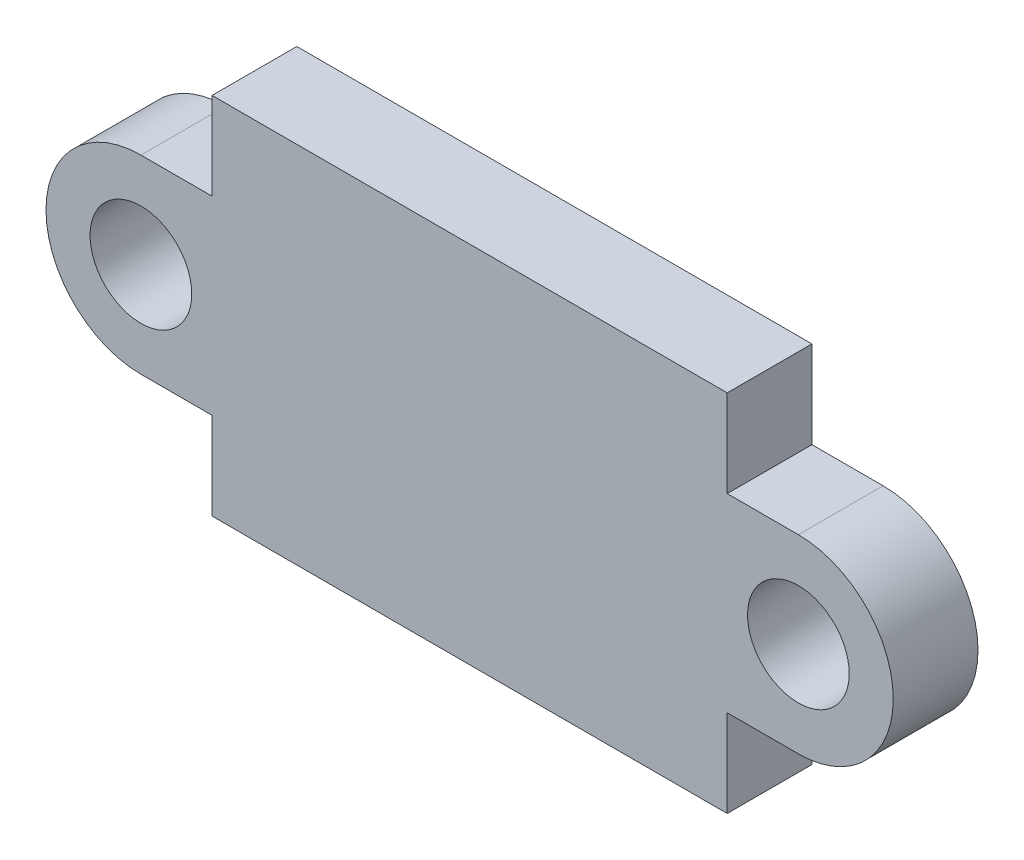
SolidWorks part; units mm, degrees
ref_plane "Ön Düzlem" through (0, 0, 0) normal (0, 0, 1) x (1, 0, 0)
ref_plane "Üst Düzlem" through (0, 0, 0) normal (0, 1, 0) x (1, 0, 0)
ref_plane "Sağ Düzlem" through (0, 0, 0) normal (1, 0, 0) x (0, 0, -1)
sketch "Sketch1" plane through (0, 0, 0) normal (0, 0, 1) x (1, 0, 0)
  line L0 (7.6, -2.8) -> (7.6, -5.375)
  line L1 (-7.6, 5.375) -> (7.6, 5.375)
  line L2 (-7.6, 5.375) -> (-7.6, 2.8)
  line L3 (-7.6, -5.375) -> (7.6, -5.375)
  line L4 (7.6, 5.375) -> (7.6, 2.8)
  line L5 (-7.6, 5.375) -> (7.6, -5.375) construction
  line L6 (-7.6, -5.375) -> (7.6, 5.375) construction
  line L7 (-7.6, -2.8) -> (-7.6, -5.375)
  line L8 (-9.7, 2.8) -> (-7.6, 2.8)
  line L9 (-9.7, -2.8) -> (-7.6, -2.8)
  line L10 (9.7, -2.8) -> (7.6, -2.8)
  line L11 (9.7, 2.8) -> (7.6, 2.8)
  arc A0 (9.7, -2.8) -> (9.7, 2.8) centre (9.7, 0) ccw
  arc A1 (-9.7, 2.8) -> (-9.7, -2.8) centre (-9.7, 0) ccw
  point P0 (0, 0)
  dimension "D3" = 5.6
  dimension "D4" = 19.4
  dimension "D1" = 15.2
  dimension "D2" = 10.75
  dimension "D5" = 9.7
extrude "Boss-Extrude1" add sketch "Sketch1" along normal blind 2.5
sketch "Sketch2" plane through (0, 0, 2.5) normal (0, 0, 1) x (1, 0, 0)
  circle A0 centre (-9.7, 0) radius 1.5
  circle A1 centre (9.7, 0) radius 1.5
extrude "Cut-Extrude1" cut sketch "Sketch2" against normal blind 2.5
